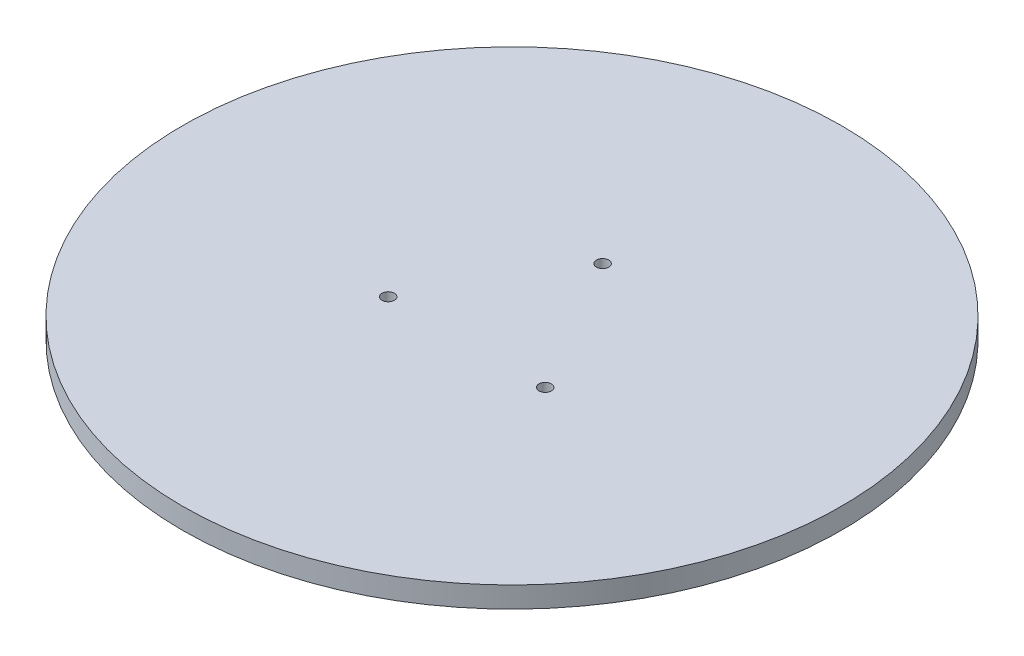
SolidWorks part; units mm, degrees
material "Copper"
ref_plane "Front Plane" through (0, 0, 0) normal (0, 0, 1) x (1, 0, 0)
ref_plane "Top Plane" through (0, 0, 0) normal (0, 1, 0) x (1, 0, 0)
ref_plane "Right Plane" through (0, 0, 0) normal (1, 0, 0) x (0, 0, -1)
sketch "Sketch1" plane through (0, 0, 0) normal (0, 1, 0) x (1, 0, 0)
  circle A0 centre (0, 0) radius 40
  dimension "D1" = 80
extrude "Boss-Extrude1" add sketch "Sketch1" along normal blind 2.54
sketch "Sketch2" plane through (0, 2.54, 0) normal (0, 1, 0) x (1, 0, 0)
  line L0 (0, 11) -> (0, -11) construction
  circle A0 centre (0, 11) radius 0.75
  circle A1 centre (9.5263, -5.5) radius 0.75
  circle A2 centre (-9.5263, -5.5) radius 0.75
  point P2 (0, 0)
  dimension "D1" = 22
  dimension "D2" = 1.5
  dimension "D3" = 3
extrude "Cut-Extrude1" cut sketch "Sketch2" against normal blind 10
sketch "Sketch3" plane through (0, 0, 0) normal (0, -1, 0) x (1, 0, 0)
  circle A0 centre (0, 0) radius 26.7
  circle A1 centre (0, 0) radius 30.7
  circle A2 centre (0, 0) radius 28.7 construction
  dimension "D1" = 4
  dimension "D2" = 2
  dimension "D3" = 57.4
extrude "Boss-Extrude2" add sketch "Sketch3" along normal blind 0.254
sketch "Sketch4" plane through (0, 2.54, 0) normal (0, 1, 0) x (1, 0, 0)
  line L0 (9.5263, -5.5) -> (14.8274, 1.4739) construction
  line L1 (14.8274, 1.4739) -> (22.0588, -7.1441)
  line L2 (6.3359, -5.5) -> (14.1145, -5.5) construction
  line L3 (14.8274, 3.2787) -> (14.8274, -0.9135) construction
  line L4 (13.2953, 0.1883) -> (20.5267, -8.4297)
  line L5 (20.5267, -8.4297) -> (22.0588, -7.1441)
  line L6 (13.2953, 0.1883) -> (14.8274, 1.4739)
  dimension "D1" = 52.76
  dimension "D2" = 40
  dimension "D3" = 8.76
  dimension "D4" = 11.25
  dimension "D5" = 2
  dimension "D6" = 90
extrude "Cut-Extrude2" [suppressed] cut sketch "Sketch4" against normal through all
fillet "Fillet1" [suppressed] radius 0.254
